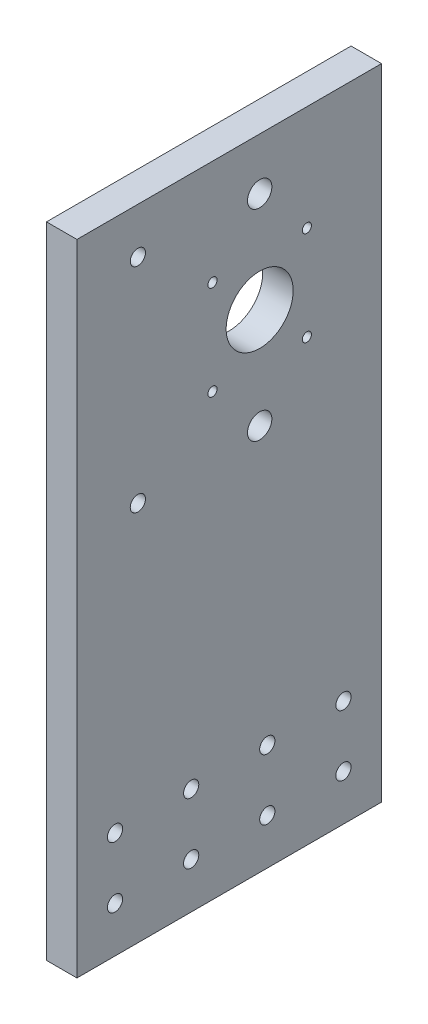
SolidWorks part; units mm, degrees
ref_plane "Front Plane" through (0, 0, 0) normal (0, 0, 1) x (1, 0, 0)
ref_plane "Top Plane" through (0, 0, 0) normal (0, 1, 0) x (1, 0, 0)
ref_plane "Right Plane" through (0, 0, 0) normal (1, 0, 0) x (0, 0, -1)
sketch "Sketch2" plane through (0, 0, 0) normal (1, 0, 0) x (0, 0, -1)
  line L0 (-60, 55) -> (40, 55) construction
  line L1 (40, -105) -> (-60, -105)
  line L2 (40, -105) -> (40, 105)
  line L3 (40, 105) -> (-60, 105)
  line L4 (-60, -105) -> (-60, 105)
  line L5 (40, -105) -> (-60, 105) construction
  line L6 (40, 105) -> (-60, -105) construction
  circle A0 centre (0, 88) radius 4
  circle A1 centre (0, 22) radius 4
  point P0 (0, 0)
  point P15 (-10, 0)
  dimension "D3" = 8
  dimension "D1" = 100
  dimension "D2" = 210
  dimension "D4" = 66
  dimension "D5" = 50
  dimension "D6" = 10
extrude "Boss-Extrude1" add sketch "Sketch2" along normal blind 10
sketch "Sketch3" plane through (10, 0, 0) normal (1, 0, 0) x (0, 0, -1)
  line L0 (-10, -105) -> (-10, -55) construction
  line L3 (-60, -105) -> (40, -105) construction
  line L5 (-35, -105) -> (-35, -55) construction
  line L6 (-10, -80) -> (-35, -80) construction
  line L8 (-35, -80) -> (-60, -80) construction
  line L9 (-60, 105) -> (-60, -105) construction
  circle A17 centre (-22.5, -70) radius 2.5
  circle A18 centre (-47.5, -70) radius 2.5
  circle A19 centre (-47.5, -90) radius 2.5
  circle A20 centre (-22.5, -90) radius 2.5
  circle A21 centre (2.5, -90) radius 2.5
  circle A22 centre (27.5, -90) radius 2.5
  circle A23 centre (27.5, -70) radius 2.5
  circle A24 centre (2.5, -70) radius 2.5
  point P15 (-22.5, -80)
  dimension "D1" = 25
  dimension "D2" = 25
  dimension "D3" = 5
  dimension "D4" = 20
extrude "mount" cut sketch "Sketch3" against normal through all
sketch "Sketch7" plane through (10, 0, 0) normal (1, 0, 0) x (0, 0, -1)
  line L0 (40, 105) -> (-60, 105) construction
  line L1 (-60, 105) -> (-60, -105) construction
  line L2 (0, 55) -> (-60, 55) construction
  line L3 (0, 88) -> (0, 22) construction
  circle A0 centre (-40, 90) radius 2.5
  circle A1 centre (-40, 20) radius 2.5
  dimension "D3" = 5
  dimension "D1" = 15
  dimension "D2" = 20
extrude "support_profile_mount" cut sketch "Sketch7" against normal through all
sketch "Sketch5" plane through (10, 0, 0) normal (1, 0, 0) x (0, 0, -1)
  line L0 (-60, 55) -> (40, 55) construction
  line L1 (-60, 105) -> (-60, -105) construction
  line L2 (40, -105) -> (40, 105) construction
  circle A0 centre (0, 22) radius 4 construction
  circle A1 centre (0, 88) radius 4 construction
  circle A2 centre (0, 55) radius 8.5
  dimension "D1" = 17
extrude "bearing_mount" [suppressed] cut sketch "Sketch5" against normal through all
sketch "Sketch4" plane through (10, 0, 0) normal (1, 0, 0) x (0, 0, -1)
  line L0 (-60, 55) -> (40, 55) construction
  line L1 (-60, 105) -> (-60, -105) construction
  line L2 (40, -105) -> (40, 105) construction
  line L3 (0, 55) -> (0, 0) construction
  circle A0 centre (0, 88) radius 4 construction
  circle A1 centre (0, 22) radius 4 construction
  circle A2 centre (0, 55) radius 11
  circle A3 centre (-15.5, 70.5) radius 1.5
  circle A4 centre (15.5, 70.5) radius 1.5
  circle A5 centre (-15.5, 39.5) radius 1.5
  circle A6 centre (15.5, 39.5) radius 1.5
  dimension "D1" = 22
  dimension "D2" = 3
  dimension "D3" = 31
  dimension "D4" = 31
extrude "stepper_mount" cut sketch "Sketch4" against normal through all
sketch "Sketch6" plane through (0, 0, 0) normal (-1, 0, 0) x (0, 0, 1)
  line L0 (0, 71.0219) -> (0, 55) construction
  line L1 (0, 55) -> (-40, 55) construction
  line L2 (-40, -105) -> (-40, 105) construction
  circle A0 centre (-15.5, 70.5) radius 2.75
  circle A1 centre (15.5, 70.5) radius 2.75
  circle A2 centre (15.5, 39.5) radius 2.75
  circle A3 centre (-15.5, 39.5) radius 2.75
  dimension "D1" = 5.5
extrude "stepper_mount_countersink" cut sketch "Sketch6" against normal blind 3
